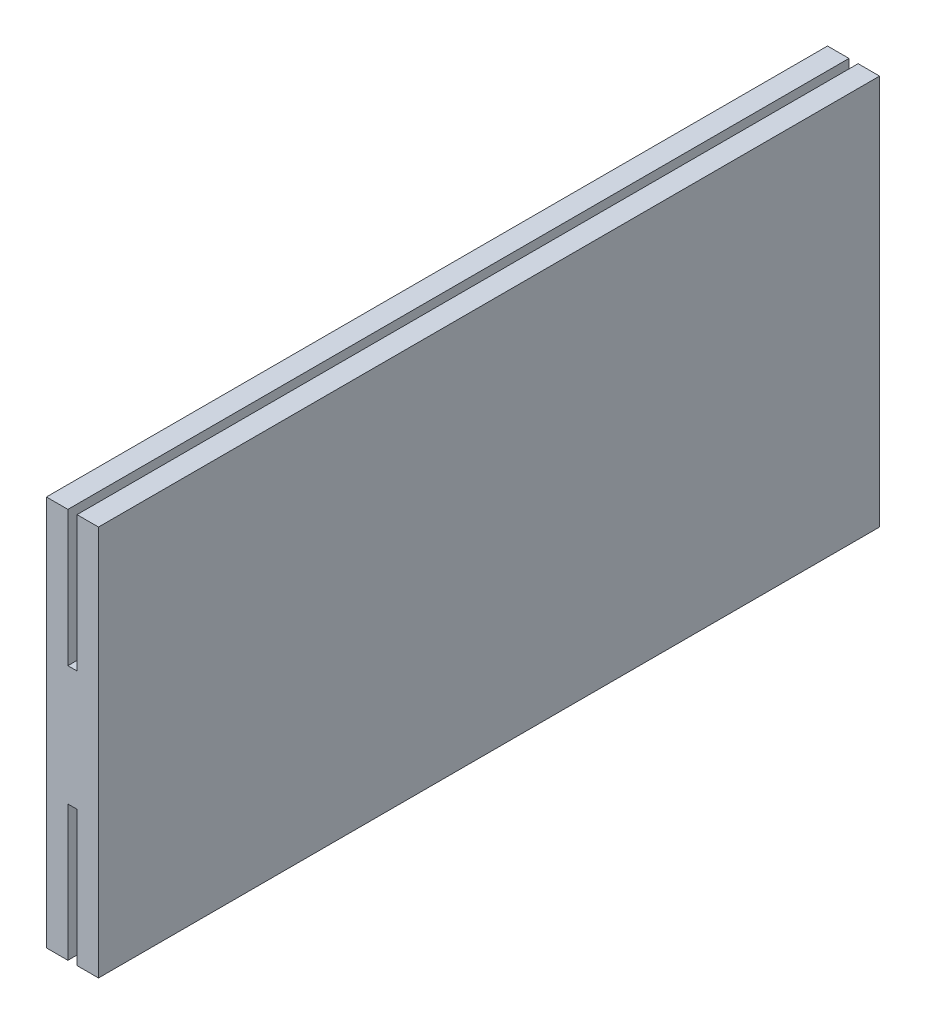
SolidWorks part; units mm, degrees
ref_plane "Front Plane" through (0, 0, 0) normal (0, 0, 1) x (1, 0, 0)
ref_plane "Top Plane" through (0, 0, 0) normal (0, 1, 0) x (1, 0, 0)
ref_plane "Right Plane" through (0, 0, 0) normal (1, 0, 0) x (0, 0, -1)
sketch "Sketch1" plane through (0, 0, 0) normal (0, 0, 1) x (1, 0, 0)
  line L1 (-1, 7.5) -> (1, 7.5)
  line L2 (-1, 7.5) -> (-1, -7.5)
  line L3 (-1, -7.5) -> (1, -7.5)
  line L4 (1, 7.5) -> (1, -7.5)
  line L5 (-1, 7.5) -> (1, -7.5) construction
  line L6 (-1, -7.5) -> (1, 7.5) construction
  line L7 (-0.175, -7.5) -> (0.175, -7.5)
  line L8 (-0.175, -7.5) -> (-0.175, -2.3)
  line L9 (-0.175, -2.3) -> (0.175, -2.3)
  line L10 (0.175, -7.5) -> (0.175, -2.3)
  line L11 (-0.175, 7.5) -> (0.175, 7.5)
  line L12 (-0.175, 7.5) -> (-0.175, 2.3)
  line L13 (-0.175, 2.3) -> (0.175, 2.3)
  line L14 (0.175, 7.5) -> (0.175, 2.3)
  point P0 (0, 0)
  point P14 (0, 2.3)
  point P15 (0, -2.3)
  dimension "D1" = 0.35
  dimension "D2" = 5.2
  dimension "D3" = 15
  dimension "D4" = 5.2
  dimension "D5" = 0.35
  dimension "D6" = 2
extrude "Boss-Extrude1" add sketch "Sketch1" along normal blind 30 contours L1 L14 L13 L12 L2 L3 L8 L9 L10 L4
